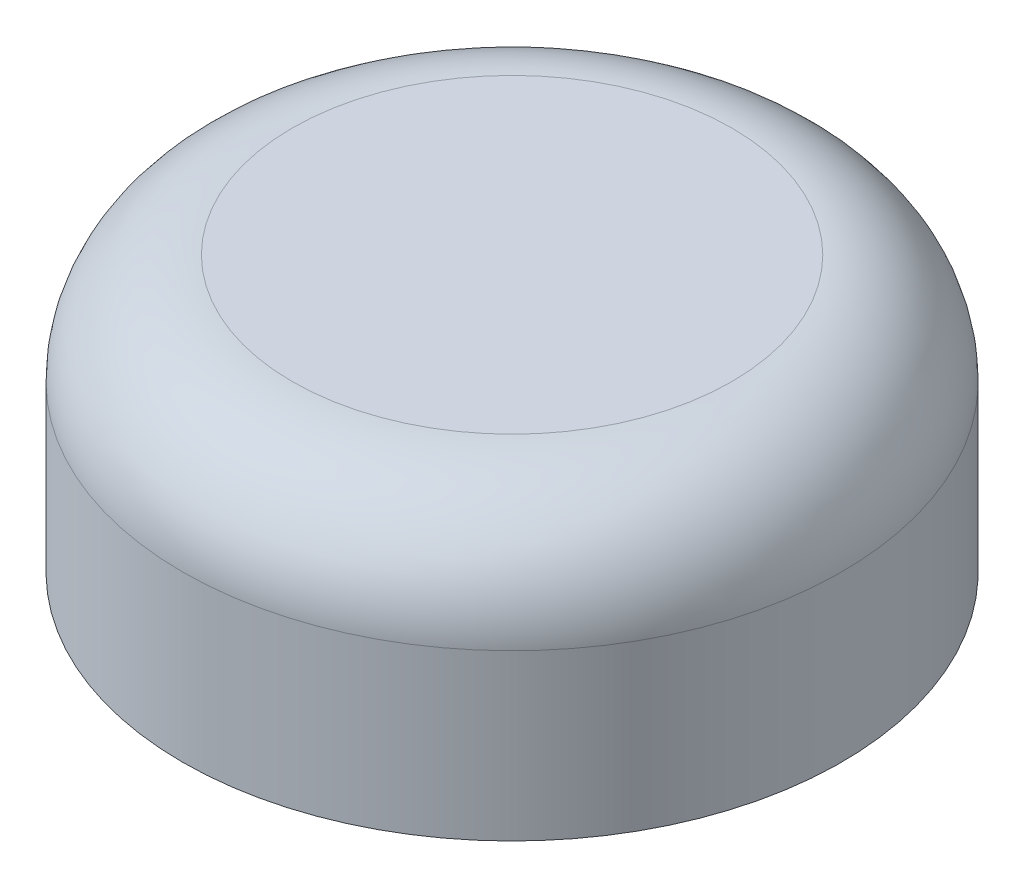
SolidWorks part; units mm, degrees
ref_plane "Front Plane" through (0, 0, 0) normal (0, 0, 1) x (1, 0, 0)
ref_plane "Top Plane" through (0, 0, 0) normal (0, 1, 0) x (1, 0, 0)
ref_plane "Right Plane" through (0, 0, 0) normal (1, 0, 0) x (0, 0, -1)
sketch "Sketch1" plane through (0, 0, 0) normal (0, 1, 0) x (1, 0, 0)
  circle A0 centre (-0.4776, 0) radius 5
  circle A1 centre (-0.4776, 0) radius 6
  dimension "D1" = 10
extrude "Boss-Extrude1" add sketch "Sketch1" along normal blind 3
sketch "Sketch2" plane through (0, 3, 0) normal (0, 1, 0) x (1, 0, 0)
  circle A0 centre (-0.4776, 0) radius 6 construction
  circle A1 centre (-0.4776, 0) radius 6
extrude "Boss-Extrude2" add sketch "Sketch2" along normal blind 2
fillet "Fillet1" radius 2 1 edges at (-0.4776, 5, 6)
